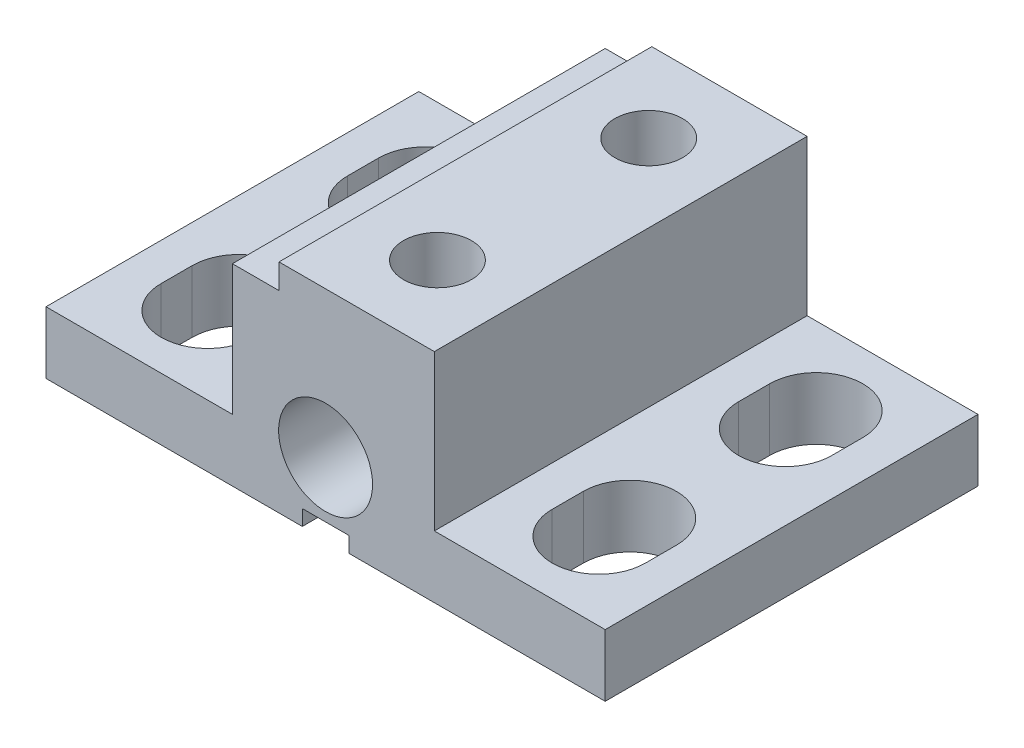
SolidWorks part; units mm, degrees
material "6061-T6 (SS)"
ref_plane "Front" through (0, 0, 0) normal (0, 0, 1) x (1, 0, 0)
ref_plane "Top" through (0, 0, 0) normal (0, 1, 0) x (1, 0, 0)
ref_plane "Right" through (0, 0, 0) normal (1, 0, 0) x (0, 0, -1)
sketch "Sketch1" plane through (0, 0, 0) normal (0, 1, 0) x (1, 0, 0)
  line L1 (0, 0) -> (-18, 0)
  line L2 (0, 0) -> (0, 12)
  line L3 (0, 12) -> (-18, 12)
  line L4 (-18, 0) -> (-18, 12)
  dimension "D1" = 12
  dimension "D2" = 18
extrude "Extrude1" add sketch "Sketch1" against normal blind 2
ref_plane "Plane1" through (0, 0, -6) normal (0, 0, -1) x (-1, 0, 0)
ref_plane "Plane2" through (-9, 0, 0) normal (1, 0, 0) x (0, 0, -1)
sketch "Sketch2" plane through (0, 0, 0) normal (0, 0, 1) x (1, 0, 0)
  line L0 (-18, -2) -> (0, -2) construction
  line L1 (-8.25, -2) -> (-9.75, -2)
  line L2 (-8.25, -2) -> (-8.25, -1.5)
  line L3 (-8.25, -1.5) -> (-9.75, -1.5)
  line L4 (-9.75, -2) -> (-9.75, -1.5)
  dimension "D1" = 8.25
  dimension "D2" = 1.5
  dimension "D3" = 0.5
extrude "Extrude2" cut sketch "Sketch2" against normal through all
sketch "Sketch3" plane through (0, 0, 0) normal (0, 1, 0) x (1, 0, 0)
  line L0 (-15.2937, 2.5) -> (-15.2937, 3.5) construction
  line L1 (-16.7937, 2.5) -> (-16.7937, 3.5)
  line L2 (-13.7937, 2.5) -> (-13.7937, 3.5)
  line L3 (-18, 12) -> (-18, 0) construction
  arc A0 (-16.7937, 2.5) -> (-13.7937, 2.5) centre (-15.2937, 2.5) ccw
  arc A1 (-13.7937, 3.5) -> (-16.7937, 3.5) centre (-15.2937, 3.5) ccw
  point P2 (-15.2937, 3)
  point P7 (-18, 6)
  dimension "D3" = 1.5
  dimension "D1" = 2.5
  dimension "D2" = 1
extrude "Extrude3" cut sketch "Sketch3" against normal through all
mirror "Mirror1" about plane through (0, 0, -6) normal (0, 0, -1) of "Extrude3"
mirror "Mirror2" about plane through (-9, 0, 0) normal (1, 0, 0) of "Mirror1", "Extrude3"
sketch "Sketch4" plane through (0, 0, 0) normal (0, 1, 0) x (1, 0, 0)
  line L0 (-18, 0) -> (0, 0) construction
  line L1 (-12, 0) -> (-5.5, 0)
  line L2 (-12, 0) -> (-12, 12)
  line L3 (-12, 12) -> (-5.5, 12)
  line L4 (-5.5, 0) -> (-5.5, 12)
  line L5 (0, 12) -> (-18, 12) construction
  line L6 (-18, 12) -> (-18, 0) construction
  line L7 (0, 0) -> (0, 12) construction
  dimension "D1" = 6
  dimension "D2" = 5.5
extrude "Extrude4" add sketch "Sketch4" along normal blind 5
sketch "Sketch5" plane through (0, 0, 0) normal (0, 0, 1) x (1, 0, 0)
  line L1 (-12, 5) -> (-10.5, 5)
  line L2 (-12, 5) -> (-12, 4.2)
  line L3 (-12, 4.2) -> (-10.5, 4.2)
  line L4 (-10.5, 5) -> (-10.5, 4.2)
  line L5 (-5.5, 5) -> (-5.5, 0) construction
  dimension "D1" = 5
  dimension "D2" = 0.8
extrude "Extrude5" cut sketch "Sketch5" against normal through all
hole_wizard "#2-56 Tapped Hole1" positions "3DSketch1" profile "Sketch6" tap size "#2-56" standard "Ansi Inch"
sketch3d "3DSketch1"
  line L0 (-5.5, 5, 0) -> (-5.5, 5, -12) construction
  point P0 (-8, 5, -2.6)
  point P2 (-8, 5, -9.4)
  dimension "D1" = 2.5
  dimension "D2" = 3.4
  dimension "D3" = 3.4
sketch "Sketch6" plane through (-8, 5, -2.6) normal (1, 0, 0) x (0, 0, 1)
  line L0 (0, 0) -> (0, 9.983)
  line L1 (0, 9.983) -> (0.889, 9.4488)
  line L2 (0.889, 9.4488) -> (0.889, 5.5372)
  line L3 (0.889, 5.5372) -> (1.0922, 5.5372)
  line L4 (1.0922, 5.5372) -> (1.0922, 0)
  line L5 (1.0922, 0) -> (0, 0)
  line L10 (0, 9.983) -> (-0.889, 9.4488) construction
  line L11 (0, -6.35) -> (0, 107.95) construction
  dimension "Tap Drill Dia." = 1.778
  dimension "Tap Drill Depth" = 9.4488
  dimension "Thread Major Dia." = 2.1844
  dimension "Thread Depth" = 5.5372
  dimension "Drill Angle" = 118
sketch "Sketch7" plane through (0, 0, 0) normal (0, 0, 1) x (1, 0, 0)
  line L0 (-9, -1.1) -> (-9, 1.1) construction
  line L1 (-8.25, -2) -> (0, -2) construction
  circle A0 centre (-9, 0.3) radius 1.5113
  dimension "D2" = 3.0226
  dimension "D1" = 2.3
extrude "Extrude6" cut sketch "Sketch7" against normal blind 3.0226
mirror "Mirror3" about plane through (0, 0, -6) normal (0, 0, -1) of "Extrude6"
